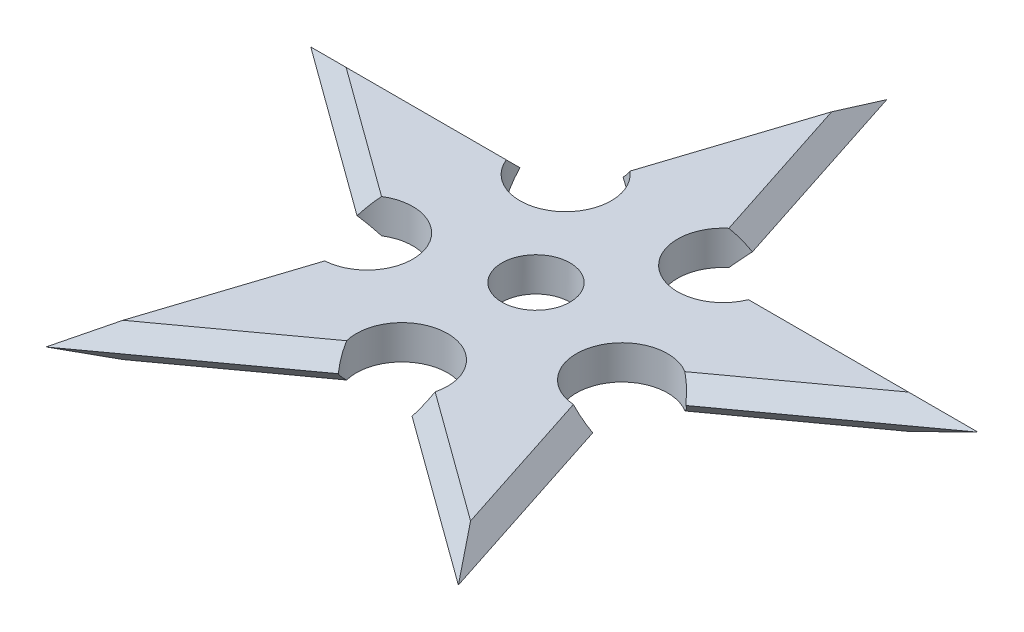
SolidWorks part; units mm, degrees
ref_plane "Front Plane" through (0, 0, 0) normal (0, 0, 1) x (1, 0, 0)
ref_plane "Top Plane" through (0, 0, 0) normal (0, 1, 0) x (1, 0, 0)
ref_plane "Right Plane" through (0, 0, 0) normal (1, 0, 0) x (0, 0, -1)
sketch "Sketch1" plane through (0, 0, 0) normal (0, 1, 0) x (1, 0, 0)
  line L0 (-29.3893, 9.5492) -> (-10.9379, 9.5492)
  line L6 (-18.1636, -25) -> (-12.4618, -7.4517)
  line L7 (18.1636, -25) -> (12.4618, -7.4517)
  line L8 (-18.1636, -25) -> (-3.2361, -14.1545)
  line L9 (-29.3893, 9.5492) -> (-14.4618, -1.2963)
  line L10 (-5.7018, 13.3534) -> (0, 30.9017)
  line L13 (5.7018, 13.3534) -> (0, 30.9017)
  line L14 (10.9379, 9.5492) -> (29.3893, 9.5492)
  line L16 (14.4618, -1.2963) -> (29.3893, 9.5492)
  line L19 (3.2361, -14.1545) -> (18.1636, -25)
  arc A1 (5.7018, 13.3534) -> (10.9379, 9.5492) centre (6.9379, 9.5492) ccw
  arc A2 (14.4618, -1.2963) -> (12.4618, -7.4517) centre (11.2257, -3.6475) ccw
  arc A3 (3.2361, -14.1545) -> (-3.2361, -14.1545) centre (0, -11.8034) ccw
  arc A4 (-12.4618, -7.4517) -> (-14.4618, -1.2963) centre (-11.2257, -3.6475) ccw
  arc A5 (-10.9379, 9.5492) -> (-5.7018, 13.3534) centre (-6.9379, 9.5492) ccw
  point P21 (0, 0)
  dimension "D1" = 5
ref_plane "Plane1" through (0, 1.5, 0) normal (0, 1, 0) x (1, 0, 0)
sketch "Sketch2" plane through (0, 1.5, 0) normal (0, 1, 0) x (1, 0, 0)
  line L0 (13.3439, -0.2544) -> (24.7727, 8.0492)
  line L1 (24.7727, 8.0492) -> (10.646, 8.0492)
  line L2 (4.3654, 12.6122) -> (0, 26.0476)
  line L3 (0, 26.0476) -> (-4.3654, 12.6122)
  line L4 (-10.646, 8.0492) -> (-24.7727, 8.0492)
  line L5 (-24.7727, 8.0492) -> (-13.3439, -0.2544)
  line L6 (-10.945, -7.6376) -> (-15.3104, -21.0729)
  line L7 (-15.3104, -21.0729) -> (-3.8816, -12.7694)
  line L8 (3.8816, -12.7694) -> (15.3104, -21.0729)
  line L9 (15.3104, -21.0729) -> (10.945, -7.6376)
  line L10 (14.4618, -1.2963) -> (29.3893, 9.5492)
  line L11 (29.3893, 9.5492) -> (10.9379, 9.5492)
  line L12 (5.7018, 13.3534) -> (0, 30.9017)
  line L13 (0, 30.9017) -> (-5.7018, 13.3534)
  line L14 (-10.9379, 9.5492) -> (-29.3893, 9.5492)
  line L15 (-29.3893, 9.5492) -> (-14.4618, -1.2963)
  line L16 (-12.4618, -7.4517) -> (-18.1636, -25)
  line L17 (-18.1636, -25) -> (-3.2361, -14.1545)
  line L18 (3.2361, -14.1545) -> (18.1636, -25)
  line L19 (18.1636, -25) -> (12.4618, -7.4517)
  line L30 (-10.9379, 9.5492) -> (-29.3893, 9.5492) construction
  line L31 (-29.3893, 9.5492) -> (-14.4618, -1.2963) construction
  line L32 (0, 30.9017) -> (-5.7018, 13.3534) construction
  line L33 (5.7018, 13.3534) -> (0, 30.9017) construction
  line L34 (29.3893, 9.5492) -> (10.9379, 9.5492) construction
  line L35 (14.4618, -1.2963) -> (29.3893, 9.5492) construction
  line L36 (18.1636, -25) -> (12.4618, -7.4517) construction
  line L37 (3.2361, -14.1545) -> (18.1636, -25) construction
  line L38 (-18.1636, -25) -> (-3.2361, -14.1545) construction
  line L39 (-12.4618, -7.4517) -> (-18.1636, -25) construction
  line L40 (0, 26.0476) -> (-3.8761, 14.1181) construction
  line L41 (3.8761, 14.1181) -> (0, 26.0476) construction
  line L42 (24.7727, 8.0492) -> (12.2294, 8.0492) construction
  line L43 (14.6249, 0.6763) -> (24.7727, 8.0492) construction
  line L44 (15.3104, -21.0729) -> (11.4343, -9.1435) construction
  line L45 (5.1626, -13.7001) -> (15.3104, -21.0729) construction
  line L46 (-15.3104, -21.0729) -> (-5.1626, -13.7001) construction
  line L47 (-11.4343, -9.1435) -> (-15.3104, -21.0729) construction
  line L48 (-24.7727, 8.0492) -> (-14.6249, 0.6763) construction
  line L49 (-12.2294, 8.0492) -> (-24.7727, 8.0492) construction
  arc A5 (14.4618, -1.2963) -> (12.4618, -7.4517) centre (11.2257, -3.6475) ccw
  arc A6 (5.7018, 13.3534) -> (10.9379, 9.5492) centre (6.9379, 9.5492) ccw
  arc A7 (-10.9379, 9.5492) -> (-5.7018, 13.3534) centre (-6.9379, 9.5492) ccw
  arc A8 (-12.4618, -7.4517) -> (-14.4618, -1.2963) centre (-11.2257, -3.6475) ccw
  arc A9 (3.2361, -14.1545) -> (-3.2361, -14.1545) centre (0, -11.8034) ccw
  arc A10 (13.3439, -0.2544) -> (10.945, -7.6376) centre (11.2257, -3.6475) ccw
  arc A11 (4.3654, 12.6122) -> (10.646, 8.0492) centre (6.9379, 9.5492) ccw
  arc A12 (-10.646, 8.0492) -> (-4.3654, 12.6122) centre (-6.9379, 9.5492) ccw
  arc A13 (-10.945, -7.6376) -> (-13.3439, -0.2544) centre (-11.2257, -3.6475) ccw
  arc A14 (3.8816, -12.7694) -> (-3.8816, -12.7694) centre (0, -11.8034) ccw
  arc A15 (-12.2294, 8.0492) -> (-3.8761, 14.1181) centre (-6.9379, 9.5492) ccw construction
  arc A16 (3.8761, 14.1181) -> (12.2294, 8.0492) centre (6.9379, 9.5492) ccw construction
  arc A17 (14.6249, 0.6763) -> (11.4343, -9.1435) centre (11.2257, -3.6475) ccw construction
  arc A18 (-11.4343, -9.1435) -> (-14.6249, 0.6763) centre (-11.2257, -3.6475) ccw construction
  arc A19 (5.1626, -13.7001) -> (-5.1626, -13.7001) centre (0, -11.8034) ccw construction
  arc A21 (5.7018, 13.3534) -> (10.9379, 9.5492) centre (6.9379, 9.5492) ccw construction
  arc A22 (-10.9379, 9.5492) -> (-5.7018, 13.3534) centre (-6.9379, 9.5492) ccw construction
  arc A23 (-12.4618, -7.4517) -> (-14.4618, -1.2963) centre (-11.2257, -3.6475) ccw construction
  arc A24 (3.2361, -14.1545) -> (-3.2361, -14.1545) centre (0, -11.8034) ccw construction
  arc A25 (14.4618, -1.2963) -> (12.4618, -7.4517) centre (11.2257, -3.6475) ccw construction
  dimension "D1" = 0
  dimension "D2" = 1.5
loft "Loft1" add profiles "Sketch2", "Sketch1"
mirror "Mirror1" about plane through (-6.9379, 0, -9.5492) normal (0, 1, 0)
sketch "Sketch3" plane through (0, 1.5, 0) normal (0, 1, 0) x (1, 0, 0)
  circle A0 centre (-6.9379, 9.5492) radius 4.02
  circle A1 centre (6.9379, 9.5492) radius 4.02
  circle A2 centre (11.2257, -3.6475) radius 4.02
  circle A3 centre (0, -11.8034) radius 4.02
  circle A4 centre (-11.2257, -3.6475) radius 4.02
  circle A5 centre (0, 0) radius 3
  point P13 (0, 0)
  dimension "D1" = 5
extrude "Cut-Extrude1" cut sketch "Sketch3" against normal blind 10
